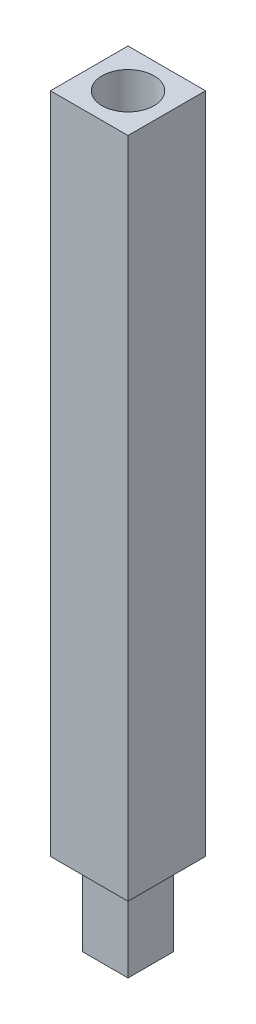
SolidWorks part; units mm, degrees
ref_plane "Front Plane" through (0, 0, 0) normal (0, 0, 1) x (1, 0, 0)
ref_plane "Top Plane" through (0, 0, 0) normal (0, 1, 0) x (1, 0, 0)
ref_plane "Right Plane" through (0, 0, 0) normal (1, 0, 0) x (0, 0, -1)
sketch "Sketch1" plane through (0, 0, 0) normal (0, 1, 0) x (1, 0, 0)
  line L1 (-5.969, 5.969) -> (5.969, 5.969)
  line L2 (-5.969, 5.969) -> (-5.969, -5.969)
  line L3 (-5.969, -5.969) -> (5.969, -5.969)
  line L4 (5.969, 5.969) -> (5.969, -5.969)
  line L9 (-5.969, 5.969) -> (5.969, -5.969) construction
  line L10 (-5.969, -5.969) -> (5.969, 5.969) construction
  point P0 (0, 0)
  dimension "D1" = 11.938
  dimension "D2" = 11.938
extrude "Boss-Extrude1" add sketch "Sketch1" along normal blind 213.106
sketch "Sketch2" plane through (0, 213.106, 0) normal (0, 1, 0) x (1, 0, 0)
  circle A0 centre (0, 0) radius 4.0005
  dimension "D1" = 8.001
sketch "Sketch3" plane through (0, 0, 0) normal (0, -1, 0) x (-1, 0, 0)
  circle A0 centre (0, 0) radius 3.6805
  dimension "D1" = 7.3609
extrude "Boss-Extrude3" add sketch "Sketch3" along normal blind 28.575
sketch "Sketch5" plane through (0, -28.575, 0) normal (0, -1, 0) x (-1, 0, 0)
  circle A0 centre (0, 0) radius 9.1375
extrude "Cut-Extrude1" cut sketch "Sketch5" against normal blind 139.573
sketch "Sketch6" plane through (0, 110.998, 0) normal (0, -1, 0) x (-1, 0, 0)
  line L1 (3.5052, 3.5052) -> (-3.5052, 3.5052)
  line L2 (3.5052, 3.5052) -> (3.5052, -3.5052)
  line L3 (3.5052, -3.5052) -> (-3.5052, -3.5052)
  line L4 (-3.5052, 3.5052) -> (-3.5052, -3.5052)
  line L5 (3.5052, 3.5052) -> (-3.5052, -3.5052) construction
  line L6 (3.5052, -3.5052) -> (-3.5052, 3.5052) construction
  point P0 (0, 0)
  dimension "D1" = 7.0104
  dimension "D2" = 7.0104
extrude "Boss-Extrude5" add sketch "Sketch6" along normal blind 12.7
extrude "Cut-Extrude2" cut sketch "Sketch2" against normal blind 11.1125
